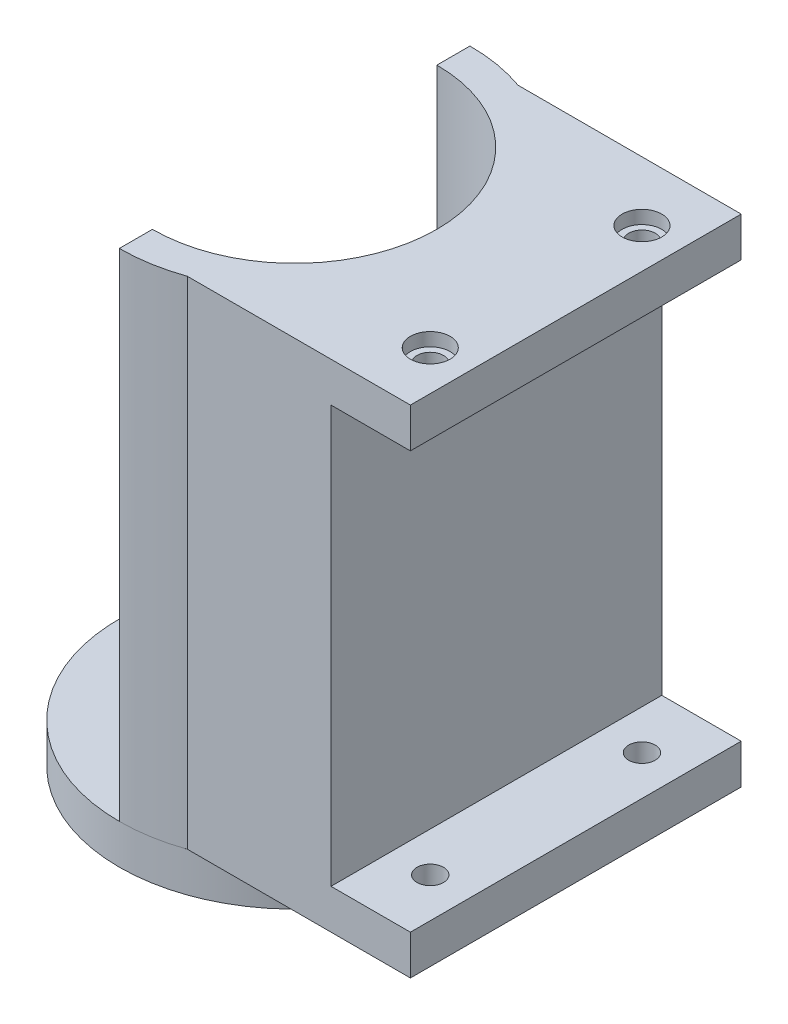
SolidWorks part; units mm, degrees
ref_plane "Front Plane" through (0, 0, 0) normal (0, 0, 1) x (1, 0, 0)
ref_plane "Top Plane" through (0, 0, 0) normal (0, 1, 0) x (1, 0, 0)
ref_plane "Right Plane" through (0, 0, 0) normal (1, 0, 0) x (0, 0, -1)
sketch "Sketch1" plane through (0, 0, 0) normal (0, 1, 0) x (1, 0, 0)
  circle A0 centre (0, 0) radius 13.25
  circle A1 centre (-8, 0) radius 1
  circle A2 centre (0, 8) radius 1
  circle A3 centre (8, 0) radius 1
  circle A4 centre (0, -8) radius 1
  point P14 (0, 0)
  dimension "D1" = 26.5
  dimension "D2" = 2
  dimension "D3" = 8
  dimension "D4" = 4
extrude "Boss-Extrude1" add sketch "Sketch1" along normal blind 3
sketch "Sketch2" plane through (0, 3, 0) normal (0, 1, 0) x (1, 0, 0)
  line L0 (0, 13.25) -> (0, 10.75)
  line L1 (0, -10.75) -> (0, -13.25)
  arc A0 (0, -13.25) -> (0, 13.25) centre (0, 0) ccw
  arc A1 (0, -10.75) -> (0, 10.75) centre (0, 0) ccw
  circle A2 centre (0, 0) radius 13.25 construction
  dimension "D1" = 21.5
ref_plane "Plane1" through (15.25, 0, 0) normal (1, 0, 0) x (0, 0, -1)
extrude "Boss-Extrude4" add sketch "Sketch2" along normal blind 37.5 separate body contours A0 L0 A1 L1
sketch "Sketch4" plane through (15.25, 0, 0) normal (1, 0, 0) x (0, 0, -1)
  line L0 (0, 40.5) -> (0, 3)
  line L8 (-13.25, 3) -> (13.25, 3) construction
  line L9 (12.5, 3) -> (-12.5, 3)
  line L10 (12.5, 3) -> (12.5, 40.5)
  line L11 (12.5, 40.5) -> (-12.5, 40.5)
  line L12 (-12.5, 3) -> (-12.5, 40.5)
  line L13 (13.25, 40.5) -> (-13.25, 40.5) construction
  point P12 (5.3792, 3)
  dimension "D1" = 25
  dimension "D2" = 12.5
extrude "Boss-Extrude5" add sketch "Sketch4" against normal up to next contours L12 L9 L0 L11 | L10 L11 L0 L9
sketch "Sketch6" plane through (15.25, 0, 0) normal (1, 0, 0) x (0, 0, -1)
  line L0 (12.5, 3) -> (12.5, 40.5) construction
  line L1 (-12.5, 40.5) -> (12.5, 40.5)
  line L2 (-12.5, 40.5) -> (-12.5, 37.5)
  line L3 (-12.5, 37.5) -> (12.5, 37.5)
  line L4 (12.5, 40.5) -> (12.5, 37.5)
  line L6 (-12.5, 3) -> (12.5, 3)
  line L7 (-12.5, 3) -> (-12.5, 6)
  line L8 (-12.5, 6) -> (12.5, 6)
  line L9 (12.5, 3) -> (12.5, 6)
  dimension "D1" = 3
  dimension "D2" = 3
extrude "Boss-Extrude6" add sketch "Sketch6" along normal blind 6
sketch "Sketch7" plane through (0, 40.5, 0) normal (0, 1, 0) x (1, 0, 0)
  line L0 (0, 0) -> (27.7138, 0) construction
  line L1 (21.25, 12.5) -> (21.25, -12.5) construction
  circle A0 centre (18.25, 8) radius 1
  circle A1 centre (18.25, -8) radius 1
  dimension "D1" = 2
  dimension "D2" = 3
  dimension "D3" = 16
extrude "Cut-Extrude1" cut sketch "Sketch7" against normal through all
sketch "Sketch8" plane through (0, 40.5, 0) normal (0, 1, 0) x (1, 0, 0)
  circle A0 centre (18.25, 8) radius 1.5
  circle A1 centre (18.25, -8) radius 1.5
  dimension "D1" = 3
  dimension "D2" = 3
extrude "Cut-Extrude2" cut sketch "Sketch8" against normal blind 1
sketch "Sketch9" plane through (0, 3, 0) normal (0, -1, 0) x (1, 0, 0)
  circle A0 centre (18.25, 8) radius 1.5
  circle A1 centre (18.25, -8) radius 1.5
  dimension "D1" = 3
  dimension "D2" = 3
extrude "Cut-Extrude3" cut sketch "Sketch9" against normal blind 1
